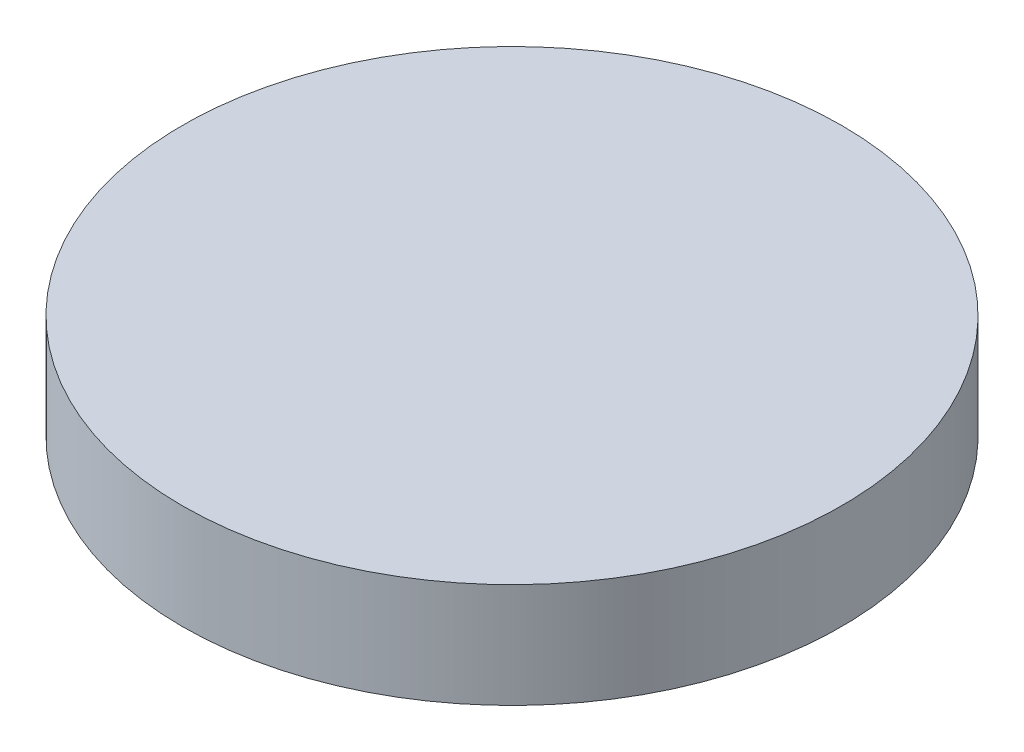
SolidWorks part; units mm, degrees
material "Balsa"
ref_plane "Front Plane" through (0, 0, 0) normal (0, 0, 1) x (1, 0, 0)
ref_plane "Top Plane" through (0, 0, 0) normal (0, 1, 0) x (1, 0, 0)
ref_plane "Right Plane" through (0, 0, 0) normal (1, 0, 0) x (0, 0, -1)
sketch "Sketch1" plane through (0, 0, 0) normal (0, 1, 0) x (1, 0, 0)
  circle A0 centre (0, 0) radius 20
  dimension "D1" = 40
extrude "Boss-Extrude1" add sketch "Sketch1" along normal blind 6.35
